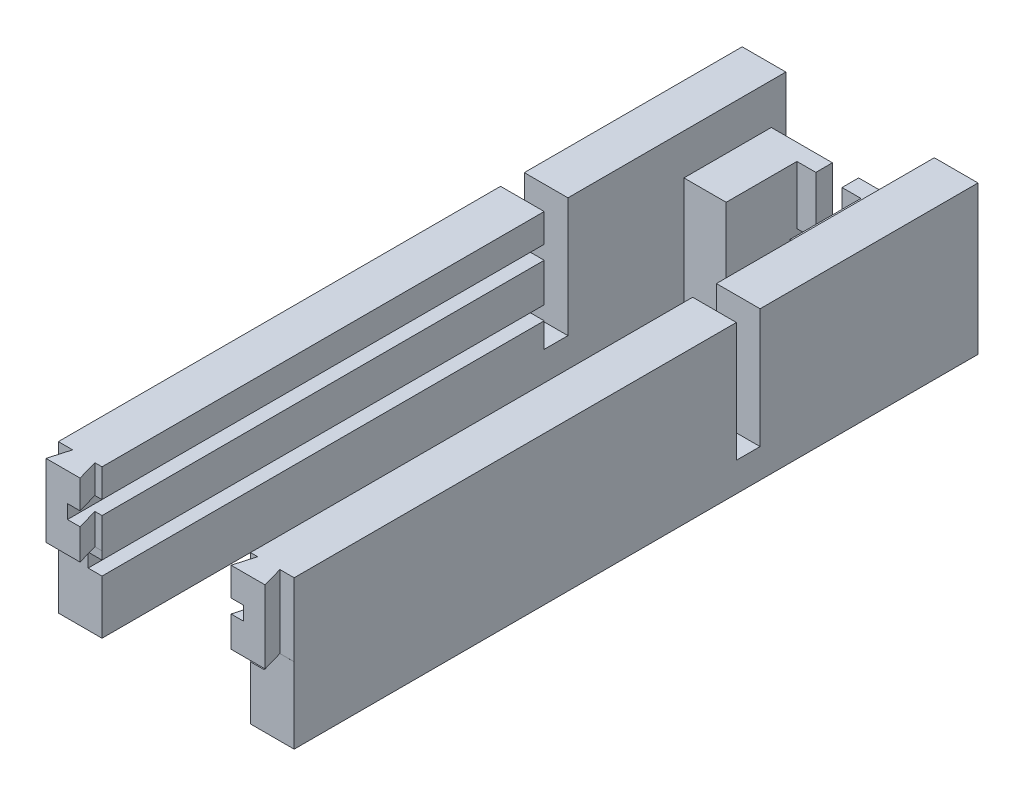
SolidWorks part; units mm, degrees
ref_plane "Front Plane" through (0, 0, 0) normal (0, 0, 1) x (1, 0, 0)
ref_plane "Top Plane" through (0, 0, 0) normal (0, 1, 0) x (1, 0, 0)
ref_plane "Right Plane" through (0, 0, 0) normal (1, 0, 0) x (0, 0, -1)
sketch "Sketch1" plane through (0, 0, 0) normal (1, 0, 0) x (0, 0, -1)
  line L1 (-64.5621, 30.5573) -> (177.4379, 30.5573)
  line L2 (-64.5621, 30.5573) -> (-64.5621, -20.4427)
  line L3 (-64.5621, -20.4427) -> (177.4379, -20.4427)
  line L4 (177.4379, 30.5573) -> (177.4379, -20.4427)
  dimension "D1" = 242
  dimension "D2" = 51
extrude "Boss-Extrude1" add sketch "Sketch1" along normal blind 15 contours L2 L3 L4 L1
sketch "Sketch26" plane through (0, 0, 0) normal (-1, 0, 0) x (0, 0, 1)
  line L1 (-172.4379, 16.5573) -> (-142.4379, 16.5573)
  line L2 (-172.4379, 16.5573) -> (-172.4379, -20.4427)
  line L3 (-172.4379, -20.4427) -> (-142.4379, -20.4427)
  line L4 (-142.4379, 16.5573) -> (-142.4379, -20.4427)
  line L5 (64.5621, -20.4427) -> (-177.4379, -20.4427) construction
  line L6 (-177.4379, 30.5573) -> (-177.4379, -20.4427) construction
  dimension "D1" = 5
  dimension "D2" = 30
  dimension "D3" = 37
extrude "Boss-Extrude3" add sketch "Sketch26" against normal blind 29.5
sketch "Sketch28" plane through (29.5, 0, 0) normal (1, 0, 0) x (0, 0, -1)
  line L0 (147.0417, -20.4427) -> (147.0417, -10.6927)
  line L1 (172.4379, -20.4427) -> (142.4379, -20.4427) construction
  line L2 (147.0417, -10.6927) -> (162.0417, -10.6927)
  line L3 (162.0417, -10.6927) -> (162.0417, -20.4427)
  line L4 (162.0417, -20.4427) -> (147.0417, -20.4427)
  dimension "D1" = 9.75
  dimension "D2" = 15
extrude "Boss-Extrude5" add sketch "Sketch28" along normal blind 4.5
sketch "Sketch29" plane through (29.5, 0, 0) normal (1, 0, 0) x (0, 0, -1)
  line L0 (172.4379, 16.5573) -> (166.7379, 16.5573)
  line L1 (142.4379, 16.5573) -> (172.4379, 16.5573) construction
  line L2 (166.7379, 16.5573) -> (166.7379, -3.4427)
  line L3 (166.7379, -3.4427) -> (172.4379, -3.4427)
  line L4 (172.4379, 16.5573) -> (172.4379, -20.4427) construction
  line L5 (172.4379, -3.4427) -> (172.4379, 16.5573)
  dimension "D1" = 20
  dimension "D2" = 5.7
extrude "Boss-Extrude6" add sketch "Sketch29" along normal blind 6.5
sketch "Sketch12" plane through (0, 30.5573, 0) normal (0, 1, 0) x (1, 0, 0)
  line L0 (0, -57.4487) -> (4.9097, -57.4487)
  line L1 (0, -64.5621) -> (0, 177.4379) construction
  line L2 (4.9097, -57.4487) -> (2.87, -64.5621)
  line L3 (15, -64.5621) -> (0, -64.5621) construction
  line L4 (2.87, -64.5621) -> (0, -64.5621)
  line L5 (0, -64.5621) -> (0, -57.4487)
  line L6 (15, -57.4487) -> (15, -64.5621)
  line L7 (15, -64.5621) -> (15, 177.4379) construction
  line L8 (15, -64.5621) -> (14.57, -64.5621)
  line L9 (14.57, -64.5621) -> (12.5303, -57.4487)
  line L10 (12.5303, -57.4487) -> (15, -57.4487)
  dimension "D1" = 7.4
  dimension "D2" = 7.4
  dimension "D3" = 106
  dimension "D4" = 106
  dimension "D5" = 11.7
  dimension "D6" = 2.87
extrude "Cut-Extrude8" cut sketch "Sketch12" against normal blind 25
sketch "Sketch13" plane through (0, -20.4427, 0) normal (0, -1, 0) x (1, 0, 0)
  line L0 (15, 64.5621) -> (15, -142.4379) construction
  line L1 (0, 64.5621) -> (15, 64.5621)
  line L2 (0, 64.5621) -> (0, 57.4521)
  line L3 (0, 57.4521) -> (15, 57.4521)
  line L4 (15, 64.5621) -> (15, 57.4521)
  dimension "D1" = 7.11
extrude "Cut-Extrude9" cut sketch "Sketch13" against normal blind 26
sketch "Sketch17" plane through (0, 30.5573, 0) normal (0, 1, 0) x (1, 0, 0)
  line L0 (15, -57.4487) -> (15, 177.4379) construction
  line L1 (0, 110.4379) -> (15, 110.4379)
  line L2 (0, 110.4379) -> (0, 102.5879)
  line L3 (0, 102.5879) -> (15, 102.5879)
  line L4 (15, 110.4379) -> (15, 102.5879)
  line L6 (0, 102.5879) -> (15, 102.5879)
  line L7 (0, 102.5879) -> (0, 94.4379)
  line L8 (0, 94.4379) -> (15, 94.4379)
  line L9 (15, 102.5879) -> (15, 94.4379)
  line M14 (15, -57.4487) -> (15, 177.4379)
  line M16 (0, 177.4379) -> (0, -57.4487)
  dimension "D1" = 7.85
  dimension "D2" = 8.15
extrude "Cut-Extrude10" cut sketch "Sketch17" against normal blind 41 contours L8 L3 M16 M14
sketch "Sketch7" plane through (0, 0, -94.4379) normal (0, 0, -1) x (-1, 0, 0)
  line L0 (-15, -20.4427) -> (-15, -1.9427)
  line L1 (-15, 2.8073) -> (-15, 16.0573)
  line L2 (-10.25, 2.8073) -> (-15, 2.8073)
  line L3 (-10.25, 2.8073) -> (-10.25, -1.9427)
  line L4 (-10.25, -1.9427) -> (-15, -1.9427)
  line L5 (-15, 2.8073) -> (-15, -1.9427)
  line L6 (-15, 30.5573) -> (-15, -20.4427) construction
  line L8 (-15, 16.0573) -> (-10.25, 16.0573)
  line L9 (-15, 16.0573) -> (-15, 20.8073)
  line L10 (-15, 20.8073) -> (-10.25, 20.8073)
  line L11 (-10.25, 16.0573) -> (-10.25, 20.8073)
  dimension "D1" = 18.5
  dimension "D2" = 4.75
  dimension "D3" = 4.75
  dimension "D4" = 13.25
  dimension "D5" = 4.75
  dimension "D6" = 4.75
extrude "Cut-Extrude5" cut sketch "Sketch7" against normal blind 165
sketch "Sketch22" plane through (0, 30.5573, 0) normal (0, 1, 0) x (1, 0, 0)
  line L0 (15, 177.4379) -> (15, 161.9379)
  line L1 (15, 102.5879) -> (15, 177.4379) construction
  line L3 (15, 161.9379) -> (8, 161.9379)
  line L4 (15, 161.9379) -> (15, 158.7879)
  line L5 (15, 158.7879) -> (8, 158.7879)
  line L6 (8, 161.9379) -> (8, 158.7879)
  line M5 (15, 102.5879) -> (15, 177.4379)
  dimension "D1" = 15.5
  dimension "D2" = 7
  dimension "D3" = 3.15
extrude "Cut-Extrude13" [suppressed] cut sketch "Sketch22" against normal blind 45 contours L3 L6 L5 M5
ref_plane "Plane1" through (40.5, 0, 0) normal (1, 0, 0) x (0, 0, -1)
sketch "Sketch18" [suppressed] plane through (0, 30.5573, 0) normal (0, 1, 0) x (1, 0, 0)
  line L0 (15, 102.5879) -> (15, 136.5879)
  line L1 (15, 102.5879) -> (15, 177.4379) construction
  line L3 (15, 136.5879) -> (10, 136.5879)
  line L4 (15, 136.5879) -> (15, 144.0879)
  line L5 (15, 144.0879) -> (10, 144.0879)
  line L6 (10, 136.5879) -> (10, 144.0879)
  line M6 (15, 102.5879) -> (15, 177.4379)
  dimension "D1" = 34
  dimension "D2" = 5
  dimension "D3" = 7.5
extrude "Cut-Extrude11" [suppressed] cut sketch "Sketch18" against normal blind 38 contours L6 L3 L5 M6
sketch "Sketch23" [suppressed] plane through (0, 0, -177.4379) normal (0, 0, -1) x (-1, 0, 0)
  line L0 (-15, -20.4427) -> (-15, 9.0573)
  line L1 (-15, 30.5573) -> (-15, -20.4427) construction
  line L3 (-15, 9.0573) -> (-10.5, 9.0573)
  line L4 (-15, 9.0573) -> (-15, 13.5573)
  line L5 (-15, 13.5573) -> (-10.5, 13.5573)
  line L6 (-10.5, 9.0573) -> (-10.5, 13.5573)
  line M5 (-15, 30.5573) -> (-15, -20.4427)
  dimension "D1" = 4.5
  dimension "D2" = 4.5
  dimension "D3" = 29.5
extrude "Cut-Extrude14" [suppressed] cut sketch "Sketch23" against normal blind 45 contours L3 L6 L5 M5
mirror "Mirror4" about plane through (40.5, 0, 0) normal (1, 0, 0) of bodies 107 113
